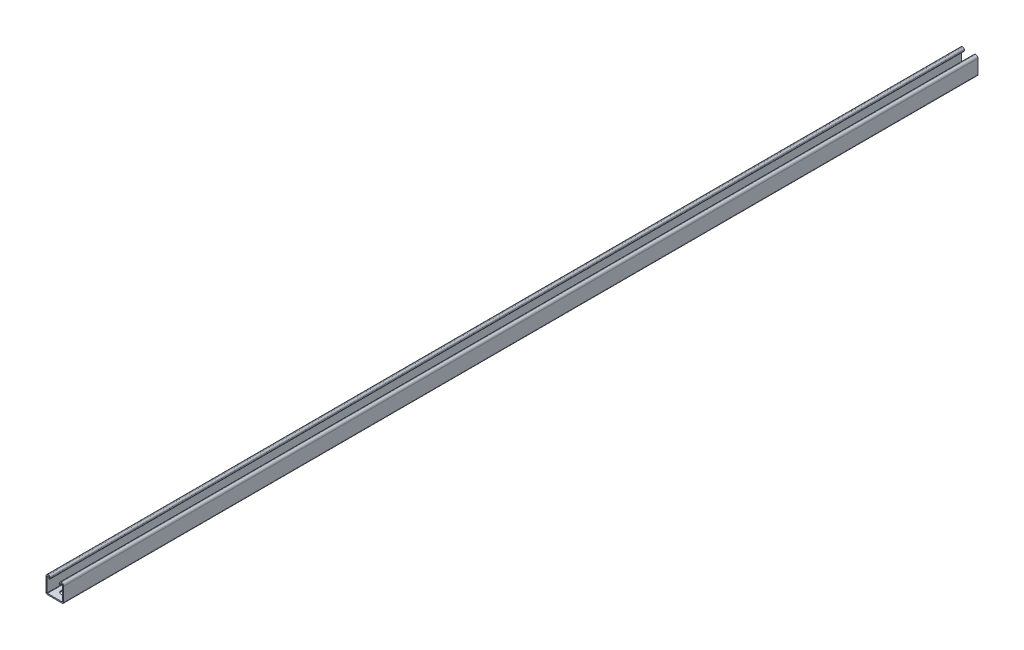
SolidWorks part; units mm, degrees
ref_plane "Front Plane" through (0, 0, 0) normal (0, 0, 1) x (1, 0, 0)
ref_plane "Top Plane" through (0, 0, 0) normal (0, 1, 0) x (1, 0, 0)
ref_plane "Right Plane" through (0, 0, 0) normal (1, 0, 0) x (0, 0, -1)
sketch "Sketch1" plane through (0, 0, 0) normal (0, 0, 1) x (1, 0, 0)
  line L0 (-20.6377, 0) -> (-17.9706, 0) construction
  line L1 (20.6377, 0) -> (17.9706, 0) construction
  line L2 (17.1769, -17.9704) -> (-17.1769, -17.9704)
  line L3 (-17.9706, -17.1766) -> (-17.9706, 15.5891)
  line L4 (-15.5894, 17.9704) -> (-14.5734, 17.9704)
  line L5 (-13.7797, 17.1766) -> (-13.7797, 14.8335)
  line L6 (-11.1127, 14.8335) -> (-11.1127, 17.1766)
  line L7 (-14.5734, 20.6374) -> (-15.5894, 20.6374)
  line L8 (-20.6377, 15.5891) -> (-20.6377, -17.1766)
  line L9 (-17.1769, -20.6374) -> (17.1769, -20.6374)
  line L10 (20.6377, 15.5891) -> (20.6377, -17.1766)
  line L11 (14.5734, 20.6374) -> (15.5894, 20.6374)
  line L12 (11.1127, 14.8335) -> (11.1127, 17.1766)
  line L13 (13.7797, 17.1766) -> (13.7797, 14.8335)
  line L14 (0, -17.9704) -> (0, -20.6374) construction
  line L15 (15.5894, 17.9704) -> (14.5734, 17.9704)
  line L16 (17.9706, -17.1766) -> (17.9706, 15.5891)
  arc A0 (-17.1769, -20.6374) -> (-20.6377, -17.1766) centre (-17.1769, -17.1766) cw
  arc A1 (-17.1769, -17.9704) -> (-17.9706, -17.1766) centre (-17.1769, -17.1766) cw
  arc A2 (-17.9706, 15.5891) -> (-15.5894, 17.9704) centre (-15.5894, 15.5891) cw
  arc A3 (-20.6377, 15.5891) -> (-15.5894, 20.6374) centre (-15.5894, 15.5891) cw
  arc A4 (-14.5734, 17.9704) -> (-13.7797, 17.1766) centre (-14.5734, 17.1766) cw
  arc A5 (-14.5734, 20.6374) -> (-11.1127, 17.1766) centre (-14.5734, 17.1766) cw
  arc A6 (-13.7797, 14.8335) -> (-11.1127, 14.8335) centre (-12.4462, 14.8335) ccw
  arc A7 (13.7797, 14.8335) -> (11.1127, 14.8335) centre (12.4462, 14.8335) cw
  arc A8 (14.5734, 20.6374) -> (11.1127, 17.1766) centre (14.5734, 17.1766) ccw
  arc A9 (14.5734, 17.9704) -> (13.7797, 17.1766) centre (14.5734, 17.1766) ccw
  arc A10 (20.6377, 15.5891) -> (15.5894, 20.6374) centre (15.5894, 15.5891) ccw
  arc A11 (17.9706, 15.5891) -> (15.5894, 17.9704) centre (15.5894, 15.5891) ccw
  arc A12 (17.1769, -17.9704) -> (17.9706, -17.1766) centre (17.1769, -17.1766) ccw
  arc A13 (17.1769, -20.6374) -> (20.6377, -17.1766) centre (17.1769, -17.1766) ccw
  dimension "D4" = 3.4608
  dimension "D5" = 5.0483
  dimension "D7" = 3.4608
  dimension "D1" = 34.3538
  dimension "D2" = 41.2748
  dimension "D3" = 2.667
  dimension "D6" = 1.016
  dimension "D8" = 2.3432
extrude "Primary Extrusion" add sketch "Sketch1" against normal blind 2133.6
sketch "Sketch58" plane through (0, -20.6374, 0) normal (0, 1, 0) x (-1, 0, 0)
  line L0 (7.1438, -29.3687) -> (7.1438, -21.4313)
  line L1 (-7.1438, -21.4313) -> (-7.1438, -29.3687)
  line L2 (0, 22.7012) -> (0, -22.7012) construction
  line L3 (-7.1438, -25.4) -> (7.1438, -25.4) construction
  line L4 (17.1769, 0) -> (-17.1769, 0) construction
  arc A0 (7.1438, -29.3687) -> (-7.1438, -29.3687) centre (0, -29.3687) cw
  arc A1 (-7.1438, -21.4313) -> (7.1438, -21.4313) centre (0, -21.4313) cw
  point P12 (0, -36.5125)
  point P13 (0, -14.2875)
  dimension "D2" = 22.225
  dimension "D1" = 14.2875
  dimension "D3" = 25.4
extrude "Slot Cut" cut sketch "Sketch58" along normal up to next (2.667 mm away) contours L0 A1 L1 A0
pattern_linear "LPattern1" count 42 spacing 50.8 along (0, 0, -1) of "Slot Cut"
ref_plane "Center Plane" through (0, 0, -1066.8) normal (0, 0, -1) x (-1, 0, 0)
